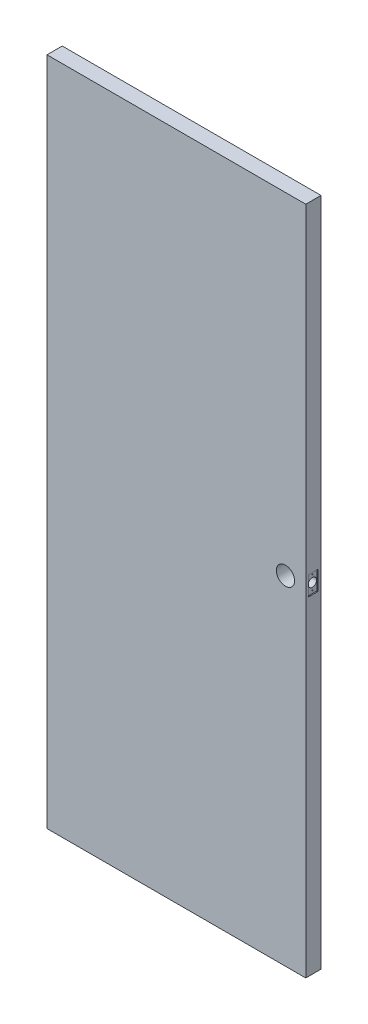
SolidWorks part; units mm, degrees
ref_plane "Front Plane" through (0, 0, 0) normal (0, 0, 1) x (1, 0, 0)
ref_plane "Top Plane" through (0, 0, 0) normal (0, 1, 0) x (1, 0, 0)
ref_plane "Right Plane" through (0, 0, 0) normal (1, 0, 0) x (0, 0, -1)
sketch "Sketch1" plane through (0, 0, 0) normal (0, 0, 1) x (1, 0, 0)
  line L1 (0, 0) -> (765, 0)
  line L2 (0, 0) -> (0, 1981)
  line L3 (0, 1981) -> (765, 1981)
  line L4 (765, 0) -> (765, 1981)
  dimension "D1" = 1981
  dimension "D2" = 765
extrude "Boss-Extrude1" add sketch "Sketch1" along normal blind 45
sketch "Sketch2" plane through (0, 0, 45) normal (0, 0, 1) x (1, 0, 0)
  line L0 (765, 0) -> (765, 1981) construction
  line L1 (0, 0) -> (765, 0) construction
  circle A0 centre (705, 1000) radius 27
  dimension "D1" = 54
  dimension "D2" = 60
  dimension "D3" = 1000
extrude "Cut-Extrude1" cut sketch "Sketch2" against normal through all
sketch "Sketch3" plane through (765, 0, 0) normal (1, 0, 0) x (0, 0, -1)
  line L0 (-45, 0) -> (-45, 1981) construction
  line L1 (-45, 0) -> (0, 0) construction
  circle A0 centre (-22.5, 1000) radius 12.5
  dimension "D1" = 22.5
  dimension "D2" = 1000
  dimension "D3" = 25
extrude "Cut-Extrude2" cut sketch "Sketch3" against normal up to next
sketch "Sketch4" plane through (765, 0, 0) normal (1, 0, 0) x (0, 0, -1)
  line L1 (-36.75, 1028.5) -> (-8.25, 1028.5)
  line L2 (-36.75, 1028.5) -> (-36.75, 971.5)
  line L3 (-36.75, 971.5) -> (-8.25, 971.5)
  line L4 (-8.25, 1028.5) -> (-8.25, 971.5)
  circle A0 centre (-22.5, 1000) radius 12.5 construction
  dimension "D1" = 28.5
  dimension "D2" = 57
  dimension "D3" = 28.5
  dimension "D4" = 14.25
extrude "Cut-Extrude3" cut sketch "Sketch4" against normal blind 3
sketch "Sketch5" plane through (762, 0, 0) normal (1, 0, 0) x (0, 0, -1)
  line L0 (-45, 0) -> (-45, 1981) construction
  circle A0 centre (-22.5, 1020.5) radius 1.5
  circle A1 centre (-22.5, 979.5) radius 1.5
  circle A2 centre (-22.5, 1000) radius 12.5 construction
  dimension "D1" = 22.5
  dimension "D2" = 22.5
  dimension "D3" = 41
  dimension "D4" = 20.5
  dimension "D5" = 3
  dimension "D6" = 3
extrude "Cut-Extrude4" cut sketch "Sketch5" against normal blind 15
